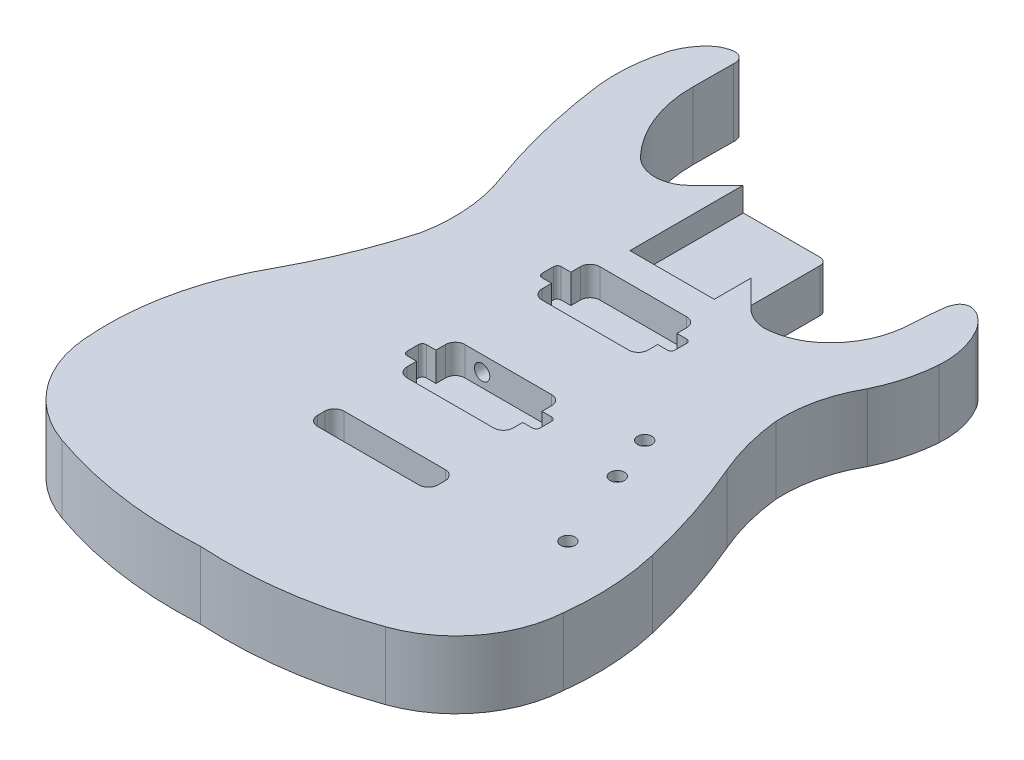
SolidWorks part; units mm, degrees
ref_plane "Front Plane" through (0, 0, 0) normal (0, 0, 1) x (1, 0, 0)
ref_plane "Top Plane" through (0, 0, 0) normal (0, 1, 0) x (1, 0, 0)
ref_plane "Right Plane" through (0, 0, 0) normal (1, 0, 0) x (0, 0, -1)
sketch "Sketch1" plane through (0, 0, 0) normal (0, 1, 0) x (1, 0, 0)
  line L0 (-27.1392, 167.7967) -> (23.2153, 167.7967)
  line L1 (27.9361, 163.0759) -> (27.9361, 117.4422)
  line L2 (27.9361, 117.4422) -> (45.7391, 99.6392)
  line L3 (-100.0456, 207.1712) -> (-99.8441, 233.8272)
  line L4 (-44.9422, 149.9937) -> (-27.1392, 167.7967)
  line L5 (82.7193, 99.6392) -> (82.7193, -19.3085) construction
  line L6 (82.7193, -19.3085) -> (-85.0907, -19.3085) construction
  line L7 (-85.0907, -19.3085) -> (-85.0907, 145.6915) construction
  line L8 (-85.0907, 145.6915) -> (-77.3768, 149.9937) construction
  line L9 (153.8565, -73.3937) -> (82.7193, -73.3937) construction
  line L10 (82.7193, -73.3937) -> (82.7193, -19.3085) construction
  line L11 (53.299, 144.5748) -> (82.7193, 99.6392) construction
  line L12 (-85.0907, -19.3085) -> (-85.0907, -33.1703) construction
  line L13 (-85.0907, -33.1703) -> (-134.0973, -33.1703) construction
  line L14 (-85.0907, -33.1703) -> (-85.0907, -208.6095) construction
  line L15 (82.7193, -73.3937) -> (82.7193, -209.2797) construction
  arc A0 (23.2153, 167.7967) -> (27.9361, 163.0759) centre (23.2153, 163.0759) cw
  arc A1 (45.7391, 99.6392) -> (60.7176, 93.0703) centre (62.3205, 117.0868) ccw
  arc A2 (60.7176, 93.0703) -> (82.7193, 99.6392) centre (59.0636, 138.7405) ccw
  arc A3 (82.7193, 99.6392) -> (106.6912, 138.7405) centre (53.299, 144.5748) ccw
  arc A4 (106.6912, 138.7405) -> (107.7833, 154.0659) centre (-417.2012, 183.7748) ccw
  arc A5 (111.1154, 170.2802) -> (116.8452, 173.2762) centre (116.9193, 166.1571) cw
  arc A6 (107.7833, 154.0659) -> (108.8537, 164.2839) centre (-483.4648, 221.1659) ccw
  arc A7 (108.8537, 164.2839) -> (111.1154, 170.2802) centre (125.9494, 161.2605) cw
  arc A8 (116.8452, 173.2762) -> (123.3557, 170.9709) centre (114.6779, 156.8095) cw
  arc A9 (123.3557, 170.9709) -> (132.1817, 161.5855) centre (105.838, 145.6547) cw
  arc A10 (132.1817, 161.5855) -> (139.6195, 129.6788) centre (84.8295, 133.7269) cw
  arc A11 (139.6195, 129.6788) -> (129.6597, 92.5449) centre (37.2022, 137.2458) cw
  arc A12 (129.6597, 92.5449) -> (118.0714, 43.8643) centre (206.8783, 48.4436) ccw
  arc A13 (118.0714, 43.8643) -> (129.6597, 0) centre (269.4338, 60.3892) ccw
  arc A14 (129.6597, 0) -> (153.8565, -73.3937) centre (-267.8062, -171.7244) cw
  arc A15 (153.8565, -73.3937) -> (157.3016, -135.3672) centre (-21.1503, -114.2048) cw
  arc A16 (157.3016, -135.3672) -> (106.6912, -202.0326) centre (81.3133, -130.2228) cw
  arc A17 (106.6912, -202.0326) -> (0, -217.0694) centre (16.1969, 54.0318) cw
  arc A18 (0, -217.0694) -> (-106.5097, -202.0326) centre (-15.9405, 54.7565) cw
  arc A19 (-106.5097, -202.0326) -> (-156.6846, -137.3943) centre (-81.3557, -130.714) cw
  arc A20 (-156.6846, -137.3943) -> (-134.0973, -33.1703) centre (21.9647, -121.5514) cw
  arc A21 (-134.0973, -33.1703) -> (-106.5097, 34.4668) centre (-428.375, 126.3034) ccw
  arc A22 (-106.5097, 34.4668) -> (-111.5361, 92.5449) centre (-210.5758, 54.7169) ccw
  arc A23 (-111.5361, 92.5449) -> (-132.0406, 177.2325) centre (257.2398, 226.6586) cw
  arc A24 (-132.0406, 177.2325) -> (-127.8951, 220.8547) centre (-23.5798, 188.9334) cw
  arc A25 (-127.8951, 220.8547) -> (-117.6515, 236.1122) centre (-91.0293, 207.1712) cw
  arc A26 (-117.6515, 236.1122) -> (-106.7274, 241.1419) centre (-104.3977, 221.7041) cw
  arc A27 (-106.7274, 241.1419) -> (-99.8441, 233.8272) centre (-106.1946, 234.7473) cw
  arc A28 (-44.9422, 149.9937) -> (-77.3768, 149.9937) centre (-61.1595, 166.211) cw
  arc A29 (-77.3768, 149.9937) -> (-100.0456, 207.1712) centre (-18.0853, 206.583) cw
  dimension "D3" = 53.71
  dimension "D5" = 525.8245
  dimension "D7" = 595.0435
  dimension "D9" = 17.361
  dimension "D11" = 7.1194
  dimension "D13" = 16.6087
  dimension "D15" = 30.786
  dimension "D17" = 54.9393
  dimension "D19" = 102.6964
  dimension "D21" = 88.9249
  dimension "D23" = 152.2618
  dimension "D25" = 432.9762
  dimension "D36" = 17.5177
  dimension "D51" = 75.6245
  dimension "D53" = 272.2929
  dimension "D56" = 19.89
  dimension "D57" = 76.1622
  dimension "D59" = 271.5846
  dimension "D1" = 167.81
  dimension "D2" = 165
  dimension "D4" = 50.55
  dimension "D6" = 1.674
  dimension "D8" = 0.989
  dimension "D10" = 21.272
  dimension "D12" = 54.013
  dimension "D14" = 24.001
  dimension "D16" = 24.156
  dimension "D18" = 34.695
  dimension "D20" = 21.577
  dimension "D22" = 32.684
  dimension "D24" = 17.136
  dimension "D26" = 10.24
  dimension "D27" = 173.0329
  dimension "D28" = 33.214
  dimension "D29" = 15.3254
  dimension "D30" = 1.0921
  dimension "D31" = 10.218
  dimension "D32" = 1.0704
  dimension "D33" = 2.1673
  dimension "D34" = 16.4667
  dimension "D35" = 47.3522
  dimension "D37" = 25.3162
  dimension "D38" = 27.8585
  dimension "D39" = 102.4172
  dimension "D40" = 7.567
  dimension "D41" = 77.2186
  dimension "D42" = 44.1013
  dimension "D43" = 397.4659
  dimension "D44" = 171.7244
  dimension "D45" = 271.8259
  dimension "D46" = 15.9405
  dimension "D47" = 197.7609
  dimension "D48" = 156.062
  dimension "D49" = 88.3811
  dimension "D50" = 34.592
  dimension "D52" = 65.505
  dimension "D54" = 175.0068
  dimension "D55" = 40.8111
  dimension "D58" = 66.663
extrude "Boss-Extrude1" add sketch "Sketch1" along normal mid plane 44.45
sketch "Sketch2" plane through (0, 22.225, 0) normal (0, 1, 0) x (1, 0, 0)
  line L0 (-27.3793, 93.0812) -> (-27.3793, 167.7967)
  line L1 (-27.3793, 167.7967) -> (23.2153, 167.7967)
  line L2 (-27.3793, 93.0812) -> (28.1832, 93.0812)
  line L3 (28.1832, 93.0812) -> (28.1832, 162.8288)
  arc A0 (23.2153, 167.7967) -> (28.1832, 162.8288) centre (23.2153, 162.8288) cw
extrude "Cut-Extrude1" cut sketch "Sketch2" against normal blind 15.875
sketch "Sketch3" plane through (0, 22.225, 0) normal (0, 1, 0) x (1, 0, 0)
  line L1 (-40.873, -27.5688) -> (-34.523, -27.5688)
  line L2 (-34.523, -27.5688) -> (-34.523, -21.2188)
  line L3 (-28.173, -14.8688) -> (28.977, -14.8688)
  line L4 (35.327, -21.2188) -> (35.327, -27.5688)
  line L5 (35.327, -27.5688) -> (41.677, -27.5688)
  line L6 (44.217, -30.1088) -> (44.217, -37.7288)
  line L7 (41.677, -40.2688) -> (35.327, -40.2688)
  line L8 (35.327, -40.2688) -> (35.327, -46.6188)
  line L9 (28.977, -52.9688) -> (-28.173, -52.9688)
  line L10 (-34.523, -46.6188) -> (-34.523, -40.2688)
  line L11 (-34.523, -40.2688) -> (-40.873, -40.2688)
  line L12 (-43.413, -37.7288) -> (-43.413, -30.1088)
  arc A0 (-34.523, -21.2188) -> (-28.173, -14.8688) centre (-28.173, -21.2188) cw
  arc A1 (28.977, -14.8688) -> (35.327, -21.2188) centre (28.977, -21.2188) cw
  arc A2 (28.977, -52.9688) -> (35.327, -46.6188) centre (28.977, -46.6188) ccw
  arc A3 (-34.523, -46.6188) -> (-28.173, -52.9688) centre (-28.173, -46.6188) ccw
  arc A4 (-43.413, -30.1088) -> (-40.873, -27.5688) centre (-40.873, -30.1088) cw
  arc A5 (-43.413, -37.7288) -> (-40.873, -40.2688) centre (-40.873, -37.7288) ccw
  arc A6 (41.677, -27.5688) -> (44.217, -30.1088) centre (41.677, -30.1088) cw
  arc A7 (44.217, -37.7288) -> (41.677, -40.2688) centre (41.677, -37.7288) cw
extrude "Cut-Extrude2" cut sketch "Sketch3" against normal blind 19.05
sketch "Sketch4" plane through (0, 22.225, 0) normal (0, 1, 0) x (1, 0, 0)
  line L1 (-40.873, 61.3312) -> (-34.523, 61.3312)
  line L2 (-34.523, 61.3312) -> (-34.523, 67.6812)
  line L3 (-28.173, 74.0312) -> (28.977, 74.0312)
  line L4 (35.327, 67.6812) -> (35.327, 61.3312)
  line L5 (35.327, 61.3312) -> (41.677, 61.3312)
  line L6 (44.217, 58.7912) -> (44.217, 51.1712)
  line L7 (41.677, 48.6312) -> (35.327, 48.6312)
  line L8 (35.327, 48.6312) -> (35.327, 42.2812)
  line L9 (28.977, 35.9312) -> (-28.173, 35.9312)
  line L10 (-34.523, 42.2812) -> (-34.523, 48.6312)
  line L11 (-34.523, 48.6312) -> (-40.873, 48.6312)
  line L12 (-43.413, 51.1712) -> (-43.413, 58.7912)
  arc A0 (-34.523, 67.6812) -> (-28.173, 74.0312) centre (-28.173, 67.6812) cw
  arc A1 (28.977, 74.0312) -> (35.327, 67.6812) centre (28.977, 67.6812) cw
  arc A2 (28.977, 35.9312) -> (35.327, 42.2812) centre (28.977, 42.2812) ccw
  arc A3 (-34.523, 42.2812) -> (-28.173, 35.9312) centre (-28.173, 42.2812) ccw
  arc A4 (-43.413, 58.7912) -> (-40.873, 61.3312) centre (-40.873, 58.7912) cw
  arc A5 (-43.413, 51.1712) -> (-40.873, 48.6312) centre (-40.873, 51.1712) ccw
  arc A6 (41.677, 61.3312) -> (44.217, 58.7912) centre (41.677, 58.7912) cw
  arc A7 (44.217, 51.1712) -> (41.677, 48.6312) centre (41.677, 51.1712) cw
extrude "Cut-Extrude3" cut sketch "Sketch4" against normal blind 19.05 contours L3 A1 L4 L5 A6 L6 A7 L7 L8 A2 L9 A3 L10 L11 A5 L12 A4 L1 L2 A0
sketch "Sketch5" plane through (0, -22.225, 0) normal (0, -1, 0) x (1, 0, 0)
  line L0 (-36.2952, 111.719) -> (-36.2952, -0.295)
  line L1 (-29.9452, -6.645) -> (36.7298, -6.645)
  line L2 (43.0798, -0.295) -> (43.0798, 111.719)
  line L3 (36.7298, 118.069) -> (-29.9452, 118.069)
  arc A0 (-36.2952, 111.719) -> (-29.9452, 118.069) centre (-29.9452, 111.719) cw
  arc A1 (36.7298, 118.069) -> (43.0798, 111.719) centre (36.7298, 111.719) cw
  arc A2 (-36.2952, -0.295) -> (-29.9452, -6.645) centre (-29.9452, -0.295) ccw
  arc A3 (43.0798, -0.295) -> (36.7298, -6.645) centre (36.7298, -0.295) cw
extrude "Cut-Extrude4" cut sketch "Sketch5" against normal blind 15.875
sketch "Sketch6" plane through (0, -22.225, 0) normal (0, -1, 0) x (1, 0, 0)
  line L0 (-29.9452, 110.1188) -> (36.7298, 110.1188)
  line L1 (-29.9452, 92.669) -> (36.7298, 92.669)
  line L2 (43.0798, 99.019) -> (43.0798, 103.7688)
  line L3 (-36.2952, 103.7688) -> (-36.2952, 99.019)
  arc A0 (-29.9452, 110.1188) -> (-36.2952, 103.7688) centre (-29.9452, 103.7688) ccw
  arc A1 (-36.2952, 99.019) -> (-29.9452, 92.669) centre (-29.9452, 99.019) ccw
  arc A2 (36.7298, 110.1188) -> (43.0798, 103.7688) centre (36.7298, 103.7688) cw
  arc A3 (36.7298, 92.669) -> (43.0798, 99.019) centre (36.7298, 99.019) ccw
extrude "Cut-Extrude5" cut sketch "Sketch6" against normal through all both and the other way through all
sketch "Sketch7" plane through (0, -22.225, 0) normal (0, -1, 0) x (1, 0, 0)
  line L0 (63.3671, -12.1514) -> (108.7432, 103.8925)
  line L1 (132.399, 94.6424) -> (87.0229, -21.4014)
  arc A0 (108.7432, 103.8925) -> (132.399, 94.6424) centre (120.5711, 99.2674) cw
  arc A1 (63.3671, -12.1514) -> (87.0229, -21.4014) centre (75.195, -16.7764) ccw
extrude "Cut-Extrude6" cut sketch "Sketch7" against normal blind 38.1
sketch "Sketch9" plane through (0, 15.875, 0) normal (0, -1, 0) x (1, 0, 0)
  line L0 (-27.3793, -93.0812) -> (28.1832, -93.0812) construction
  line L1 (28.1832, -93.0812) -> (28.1832, -117.195) construction
  circle A0 centre (85.7542, 10.2922) radius 4.75
  circle A1 centre (97.268, 39.881) radius 4.75
  circle A2 centre (117.9927, 93.1408) radius 4.75
  point P8 (0, 0)
  point P9 (0, 0)
  dimension "D7" = 9.5
  dimension "D1" = 103.3734
  dimension "D2" = 29.5888
  dimension "D3" = 11.5137
  dimension "D4" = 53.2598
  dimension "D5" = 20.7247
  dimension "D6" = 57.571
extrude "Cut-Extrude7" cut sketch "Sketch9" against normal through all both and the other way through all
sketch "Sketch10" plane through (0, 0, 0) normal (0, 0, 1) x (1, 0, 0)
  circle A0 centre (-16.8124, 12.116) radius 5.08
  dimension "D1" = 10.16
extrude "Cut-Extrude8" cut sketch "Sketch10" against normal blind 38.1 and the other way blind 38.1
sketch "Sketch13" plane through (0, 22.225, 0) normal (0, 1, 0) x (1, 0, 0)
  line L2 (-52.9682, -217.1099) -> (54.0867, -2.7494) construction
ref_plane "Plane1" through (44.3886, 0, 22.1683) normal (0.8946, 0, 0.4468) x (0.4468, 0, -0.8946)
sketch "Sketch14" plane through (44.3886, 0, 22.1683) normal (0.8946, 0, 0.4468) x (0.4468, 0, -0.8946)
  line L4 (-30.3246, 12.3712) -> (-30.603, 12.3712)
  circle A0 centre (-30.3246, 12.3712) radius 5.08
  dimension "D1" = 10.16
extrude "Cut-Extrude9" cut sketch "Sketch14" along normal blind 88.9
